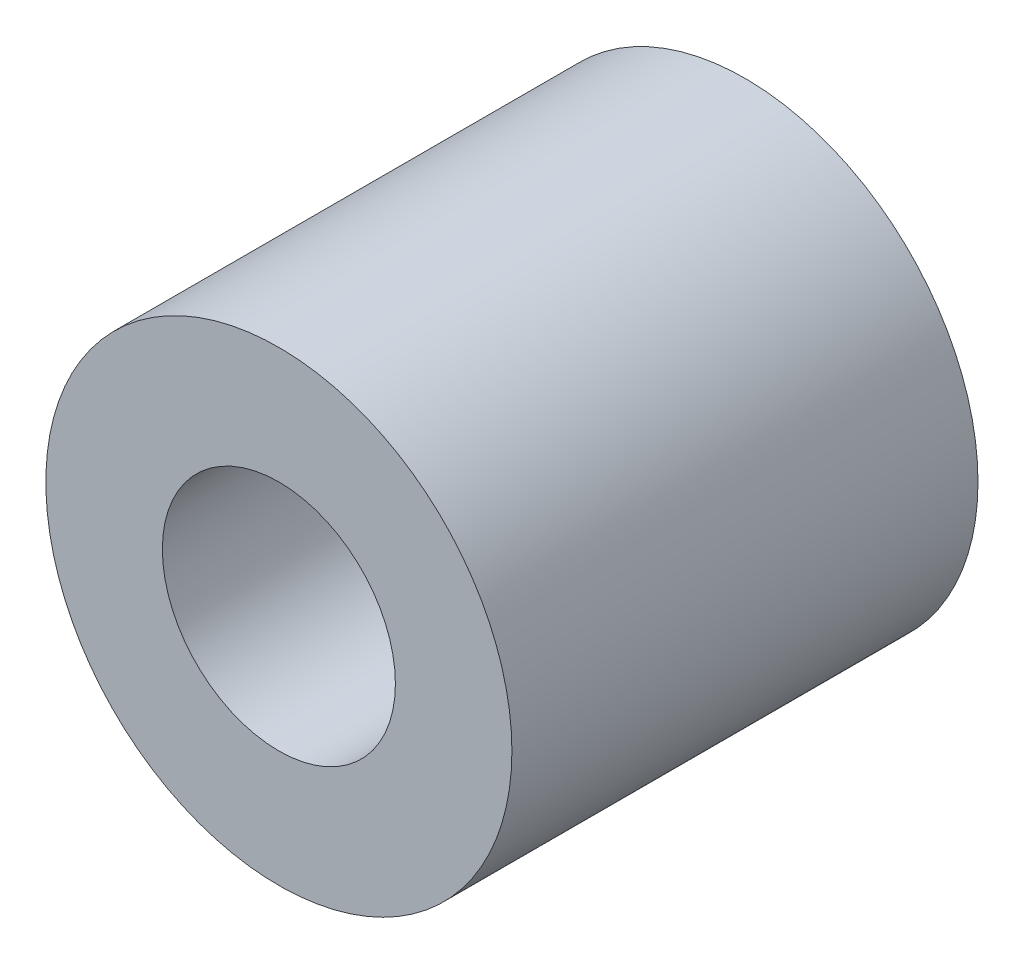
SolidWorks part; units mm, degrees
ref_plane "Front Plane" through (0, 0, 0) normal (0, 0, 1) x (1, 0, 0)
ref_plane "Top Plane" through (0, 0, 0) normal (0, 1, 0) x (1, 0, 0)
ref_plane "Right Plane" through (0, 0, 0) normal (1, 0, 0) x (0, 0, -1)
sketch "Sketch1" plane through (0, 0, 0) normal (0, 0, 1) x (1, 0, 0)
  circle A0 centre (0, 0) radius 12.7
  dimension "D1" = 25.4
extrude "Boss-Extrude1" add sketch "Sketch1" along normal blind 25.4
sketch "Sketch2" plane through (0, 0, 25.4) normal (0, 0, 1) x (1, 0, 0)
  circle A0 centre (0, 0) radius 6.35
  dimension "D1" = 12.7
extrude "Cut-Extrude1" cut sketch "Sketch2" against normal blind 25.4
